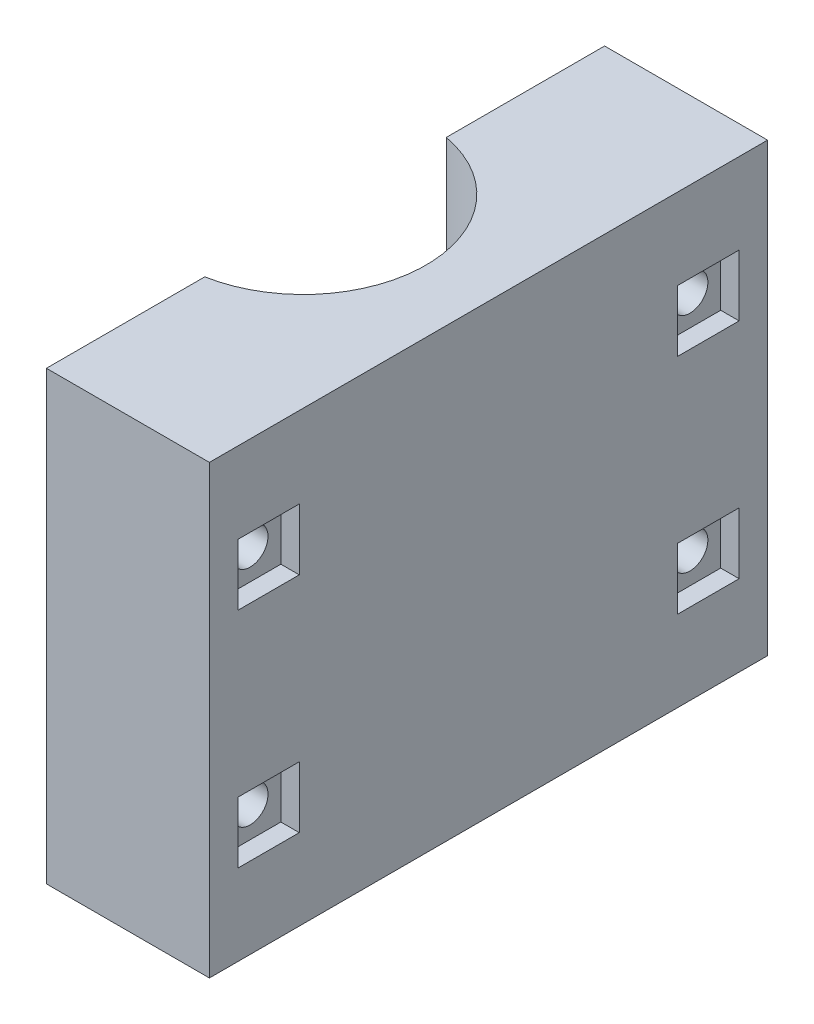
SolidWorks part; units mm, degrees
ref_plane "Front Plane" through (0, 0, 0) normal (0, 0, 1) x (1, 0, 0)
ref_plane "Top Plane" through (0, 0, 0) normal (0, 1, 0) x (1, 0, 0)
ref_plane "Right Plane" through (0, 0, 0) normal (1, 0, 0) x (0, 0, -1)
sketch "Sketch1" plane through (0, 0, 0) normal (0, 1, 0) x (1, 0, 0)
  line L3 (0, 0) -> (18.542, 0)
  line L8 (0, 0) -> (0, 63.5)
  line L9 (0, 63.5) -> (18.542, 63.5)
  line L10 (18.542, 0) -> (18.542, 63.5)
  dimension "D1" = 63.5
  dimension "D2" = 18.542
ref_plane "Plane1" through (0, 50.8, 0) normal (0, 1, 0) x (1, 0, 0)
extrude "Boss-Extrude1" add sketch "Sketch1" along normal up to surface (50.8 mm away) up to plane "Plane1"
sketch "Sketch2" plane through (0, 50.8, 0) normal (0, 1, 0) x (1, 0, 0)
  line L0 (0, 0) -> (0, 63.5) construction
  line L2 (-2.54, 45.72) -> (-2.54, 17.78)
  line L5 (-2.54, 31.75) -> (0, 31.75) construction
  arc A1 (-2.54, 45.72) -> (-2.54, 17.78) centre (-2.54, 31.75) cw
  dimension "D1" = 2.54
  dimension "D2" = 13.97
extrude "Cut-Extrude1" cut sketch "Sketch2" against normal up to surface (50.8 mm away) up to face at (9.271, 0, -31.75)
sketch "Sketch4" plane through (18.542, 0, 0) normal (1, 0, 0) x (0, 0, -1)
  line L0 (63.5, 0) -> (63.5, 50.8) construction
  line L1 (17.3897, 50.8) -> (-17.3897, 50.8) construction
  line L2 (63.5, 50.8) -> (63.5, 0) construction
  line L3 (63.5, 25.4) -> (63.5, 50.8) construction
  line L4 (63.5, 25.4) -> (31.75, 25.4) construction
  line L5 (56.769, 25.4) -> (56.769, 50.8) construction
  line L6 (0, 50.8) -> (63.5, 50.8) construction
  line L7 (31.75, 25.4) -> (31.75, 50.8) construction
  circle A0 centre (56.769, 38.1) radius 2.032
  circle A1 centre (56.769, 12.7) radius 2.032
  circle A2 centre (6.731, 38.1) radius 2.032
  circle A3 centre (6.731, 12.7) radius 2.032
  point P15 (56.769, 38.1)
  point P19 (31.75, 50.8)
  dimension "D2" = 4.064
  dimension "D1" = 6.731
extrude "Cut-Extrude3" cut sketch "Sketch4" against normal up to surface (18.542 mm away) up to face at (0, 25.4, -9.0064)
ref_plane "Plane2" through (16.4465, 0, 0) normal (1, 0, 0) x (0, 0, -1)
sketch "Sketch6" plane through (18.542, 0, 0) normal (1, 0, 0) x (0, 0, -1)
  line L0 (0, 25.4) -> (63.5, 25.4) construction
  line L1 (60.2615, 34.6075) -> (53.2765, 34.6075)
  line L2 (60.2615, 34.6075) -> (60.2615, 41.5925)
  line L3 (60.2615, 41.5925) -> (53.2765, 41.5925)
  line L4 (53.2765, 34.6075) -> (53.2765, 41.5925)
  line L5 (60.2615, 34.6075) -> (53.2765, 41.5925) construction
  line L6 (60.2615, 41.5925) -> (53.2765, 34.6075) construction
  line L7 (0, 50.8) -> (0, 0) construction
  line L8 (63.5, 50.8) -> (63.5, 0) construction
  line L9 (31.75, 0) -> (31.75, 50.8) construction
  line L10 (0, 0) -> (63.5, 0) construction
  line L11 (17.3897, 50.8) -> (-17.3897, 50.8) construction
  line L12 (60.2615, 9.2075) -> (53.2765, 9.2075)
  line L13 (53.2765, 16.1925) -> (53.2765, 9.2075)
  line L14 (60.2615, 16.1925) -> (53.2765, 16.1925)
  line L15 (60.2615, 16.1925) -> (60.2615, 9.2075)
  line L16 (3.2385, 41.5925) -> (10.2235, 41.5925)
  line L17 (10.2235, 34.6075) -> (10.2235, 41.5925)
  line L18 (3.2385, 34.6075) -> (10.2235, 34.6075)
  line L19 (3.2385, 34.6075) -> (3.2385, 41.5925)
  line L20 (3.2385, 16.1925) -> (3.2385, 9.2075)
  line L21 (3.2385, 16.1925) -> (10.2235, 16.1925)
  line L22 (10.2235, 16.1925) -> (10.2235, 9.2075)
  line L23 (3.2385, 9.2075) -> (10.2235, 9.2075)
  point P0 (56.769, 38.1)
  dimension "D1" = 6.985
extrude "Cut-Extrude4" cut sketch "Sketch6" against normal up to surface (2.0955 mm away)
